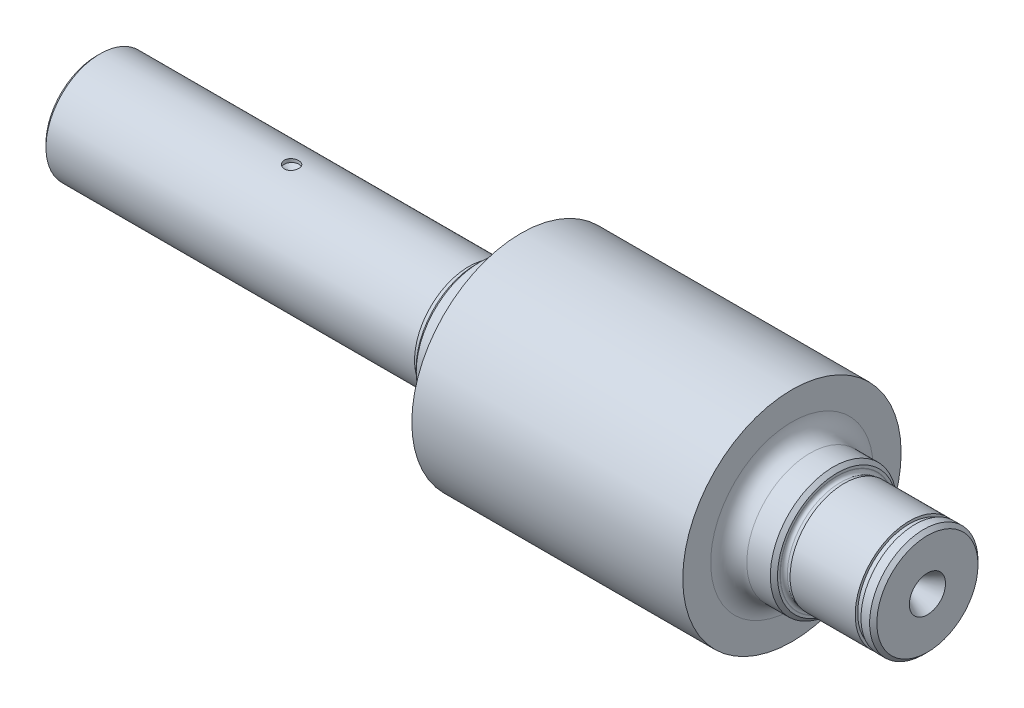
SolidWorks part; units mm, degrees
material "Plain Carbon Steel"
ref_plane "Front Plane" through (0, 0, 0) normal (0, 0, 1) x (1, 0, 0)
ref_plane "Top Plane" through (0, 0, 0) normal (0, 1, 0) x (1, 0, 0)
ref_plane "Right Plane" through (0, 0, 0) normal (1, 0, 0) x (0, 0, -1)
sketch "Sketch1" plane through (0, 0, 0) normal (0, 0, 1) x (1, 0, 0)
  line L0 (230, 0) -> (0, 0)
  line L1 (0, 0) -> (0, 15)
  line L2 (0, 15) -> (103.0272, 15)
  line L4 (105, 17.5) -> (117.5, 17.5)
  line L5 (117.5, 17.5) -> (117.5, 30.225)
  line L6 (117.5, 30.225) -> (192.5, 30.225)
  line L7 (192.5, 30.225) -> (192.5, 17.5)
  line L8 (192.5, 17.5) -> (205, 17.5)
  line L9 (205, 17.5) -> (205, 15.8)
  line L10 (206.9728, 15) -> (225, 15)
  line L11 (230, 15) -> (230, 0)
  line L12 (103.0272, 15) -> (104.0451, 14.7273)
  line L13 (105, 15.8) -> (105.0249, 15.7071)
  line L14 (104.7784, 14.7) -> (102.6077, 14.7) construction
  line L15 (105, 15.8) -> (105, 17.5)
  line L16 (105.0522, 16.2247) -> (105.0522, 15.1751) construction
  line L17 (155, 30.225) -> (155, -5.7794) construction
  line L18 (206.9728, 15) -> (205.9549, 14.7273)
  line L19 (205, 15.8) -> (204.9751, 15.7071)
  line L20 (226.6, 15) -> (226.6, 14.3)
  line L21 (226.6, 14.3) -> (225, 14.3)
  line L22 (225, 14.3) -> (225, 15)
  line L23 (226.6, 15) -> (230, 15)
  arc A0 (104.0451, 14.7273) -> (105.0249, 15.7071) centre (104.2522, 15.5) ccw
  arc A1 (205.9549, 14.7273) -> (204.9751, 15.7071) centre (205.7478, 15.5) cw
  point P18 (104.2522, 14.7)
  point P23 (105.0522, 15.5)
  point P24 (105.0522, 15.5)
  dimension "D10" = 0.8
  dimension "D1" = 15
  dimension "D2" = 17.5
  dimension "D3" = 30.225
  dimension "D4" = 0.0522
  dimension "D5" = 75
  dimension "D6" = 12.5
  dimension "D7" = 3.4
  dimension "D8" = 0.3
  dimension "D9" = 60
  dimension "D11" = 15
  dimension "D12" = 1.1
  dimension "D13" = 20
  dimension "D14" = 1.6
  dimension "D15" = 14.3
  dimension "D16" = 105
revolve "Revolve1" add sketch "Sketch1" angle 360 about L0
fillet "Fillet1" radius 5 2 edges at (192.5, 0, -17.5) (117.5, 0, -17.5)
chamfer "Chamfer1" distance 1 angle 45 2 edges at (105, 0, -17.5) (205, 0, -17.5)
sketch "Sketch2" plane through (117.5, 0, 0) normal (-1, 0, 0) x (0, 0, 1)
  line L0 (0, 0) -> (0, 32.8609) construction
  arc A1 (-11.4507, 21.0467) -> (0, 23.96) centre (0, 0) cw
  dimension "D1" = 23.96
chamfer "Chamfer3" distance 1 angle 45 2 edges at (0, 0, -15) (230, 0, -15)
ref_plane "Plane1" through (0, -10.9, 0) normal (0, 1, 0) x (1, 0, 0)
sketch "Sketch3" plane through (0, -10.9, 0) normal (0, 1, 0) x (1, 0, 0)
  line L1 (0, 4) -> (60, 4)
  line L2 (0, -4) -> (60, -4)
  line L3 (0, -4) -> (0, 4)
  line L4 (60, 4) -> (60, -4)
  dimension "D1" = 60
  dimension "D2" = 8
extrude "Cut-Extrude3" cut sketch "Sketch3" against normal up to next
sketch "Sketch4" plane through (0, 0, 0) normal (0, 0, 1) x (1, 0, 0)
  line L0 (54, 15) -> (54, 12.8453)
  line L1 (103.0272, 15) -> (1, 15) construction
  line L2 (54, 12.8453) -> (52, 14)
  line L3 (52, 14) -> (52, 15)
  line L4 (52, 15) -> (54, 15)
  line L7 (0, 14) -> (0, -13.4164) construction
  dimension "D1" = 60
  dimension "D2" = 1
  dimension "D3" = 2
  dimension "D4" = 54
revolve "Cut-Revolve1" cut sketch "Sketch4" angle 360 about L0
sketch "Sketch8" plane through (0, 0, 0) normal (0, 1, 0) x (1, 0, 0)
  line L0 (0, 5) -> (5.1962, 2)
  line L1 (0, 14) -> (0, -14) construction
  line L2 (5.1962, 2) -> (9, 2)
  line L3 (9, 2) -> (9.8284, 0)
  line L4 (9.8284, 0) -> (0, 0)
  line L5 (0, 0) -> (0, 5)
  dimension "D1" = 2
  dimension "D2" = 5
  dimension "D3" = 30
  dimension "D4" = 9
  dimension "D5" = 67.5
revolve "Cut-Revolve2" cut sketch "Sketch8" angle 360 about L4
ref_plane "Plane2" through (115, 0, 0) normal (-1, 0, 0) x (0, 0, 1)
mirror "Mirror1" about plane through (115, 0, 0) normal (-1, 0, 0) of "Cut-Revolve2"
hole_wizard "Ø2.5mm Dowel Hole1" positions "Sketch12" profile "Sketch13" hole size "Ø2.5" standard "ISO"
sketch "Sketch12" plane through (0, -10.9, 0) normal (0, -1, 0) x (-1, 0, 0)
  line L0 (0, 4) -> (0, -4) construction
  point P0 (-30, 0)
  dimension "D1" = 30
sketch "Sketch13" plane through (30, -10.9, 0) normal (1, 0, 0) x (0, 0, -1)
  line L0 (0, 0) -> (0, 5.7511)
  line L1 (0, 5.7511) -> (1.25, 5)
  line L2 (1.25, 5) -> (1.25, 0)
  line L5 (1.25, 0) -> (0, 0)
  line L10 (0, 5.7511) -> (-1.25, 5) construction
  line L11 (0, -6.35) -> (0, 107.95) construction
  dimension "Hole Dia." = 2.5
  dimension "Hole Depth" = 5
  dimension "Drill Angle" = 118
sketch "Sketch14" plane through (0, 0, 0) normal (0, 0, 1) x (1, 0, 0)
  line L0 (60, -15) -> (60, -10.9)
  line L1 (60, -14.4568) -> (60, -15) construction
  line L2 (33.2475, -10.9) -> (-33.2475, -10.9) construction
  line L3 (60, -15) -> (70, -15)
  line L4 (60, -10.9) -> (54.5842, -10.9) construction
  arc A0 (60, -10.9) -> (70, -15) centre (60, -25.1451) cw
  dimension "D1" = 10
  dimension "D2" = 4.1
extrude "Cut-Extrude4" cut sketch "Sketch14" against normal up to surface and the other way up to surface up to face at (24.3, -12.9301, -4) other way up to face at (24.1, -12.722, 4)
